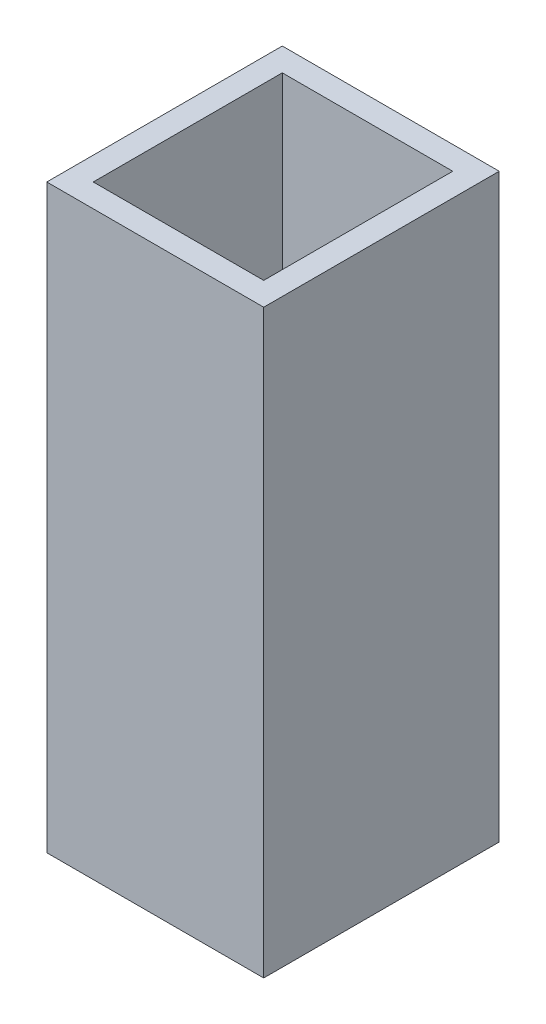
SolidWorks part; units mm, degrees
material "ABS PC"
ref_plane "Front" through (0, 0, 0) normal (0, 0, 1) x (1, 0, 0)
ref_plane "Top" through (0, 0, 0) normal (0, 1, 0) x (1, 0, 0)
ref_plane "Right" through (0, 0, 0) normal (1, 0, 0) x (0, 0, -1)
sketch "Sketch1" plane through (0, 0, 0) normal (0, 1, 0) x (1, 0, 0)
  line L0 (-9.335, 10.135) -> (9.335, -10.135) construction
  line L1 (-9.335, 10.135) -> (9.335, 10.135)
  line L2 (-9.335, 10.135) -> (-9.335, -10.135)
  line L3 (-9.335, -10.135) -> (9.335, -10.135)
  line L4 (9.335, 10.135) -> (9.335, -10.135)
  point P4 (0, 0)
  dimension "D1" = 20.27
  dimension "D2" = 18.67
extrude "Extrude1" add sketch "Sketch1" along normal blind 50
shell "Shell1" thickness 2
sketch "Sketch5" plane through (0, 0, 0) normal (0, -1, 0) x (1, 0, 0)
  line L0 (7.5, 8.5) -> (-7.5, -8.5) construction
  line L1 (-8, -9) -> (-7, -9)
  line L2 (-8, -9) -> (-8, -8)
  line L3 (-8, -8) -> (-7, -8)
  line L4 (-7, -9) -> (-7, -8)
  line L5 (7.5, 8.5) -> (-7.5, 8.5) construction
  line L6 (7.5, 8.5) -> (7.5, -8.5) construction
  line L7 (7.5, -8.5) -> (-7.5, -8.5) construction
  line L8 (-7.5, 8.5) -> (-7.5, -8.5) construction
  line L9 (-8, -8) -> (-7, -9) construction
  point P8 (0, 0)
  point P9 (-7.5, -8.5)
  dimension "D1" = 1
  dimension "D2" = 17
  dimension "D3" = 15
extrude "Extrude3" cut sketch "Sketch5" against normal up to surface (2 mm away) up to face at (0, 2, 0)
pattern_linear "LPattern1" count 8 spacing 2.1429 along (1, 0, 0) of "Extrude3"
pattern_linear "LPattern2" count 9 spacing 2.125 along (0, 0, 1) of "LPattern1", "Extrude3"
sketch "Sketch6" plane through (0, 2, 0) normal (0, 1, 0) x (1, 0, 0)
  line L9 (-8.335, 9.135) -> (-8.335, -9.135)
  line L10 (8.335, 9.135) -> (-8.335, 9.135)
  line L11 (8.335, -9.135) -> (8.335, 9.135)
  line L12 (-8.335, -9.135) -> (8.335, -9.135)
  line L13 (-8.335, 9.135) -> (-8.335, -9.135)
  line L14 (8.335, 9.135) -> (-8.335, 9.135)
  line L15 (8.335, -9.135) -> (8.335, 9.135)
  line L16 (-8.335, -9.135) -> (8.335, -9.135)
  dimension "D1" = 1
extrude "Cut-Extrude1" cut sketch "Sketch6" along normal blind 1.5
